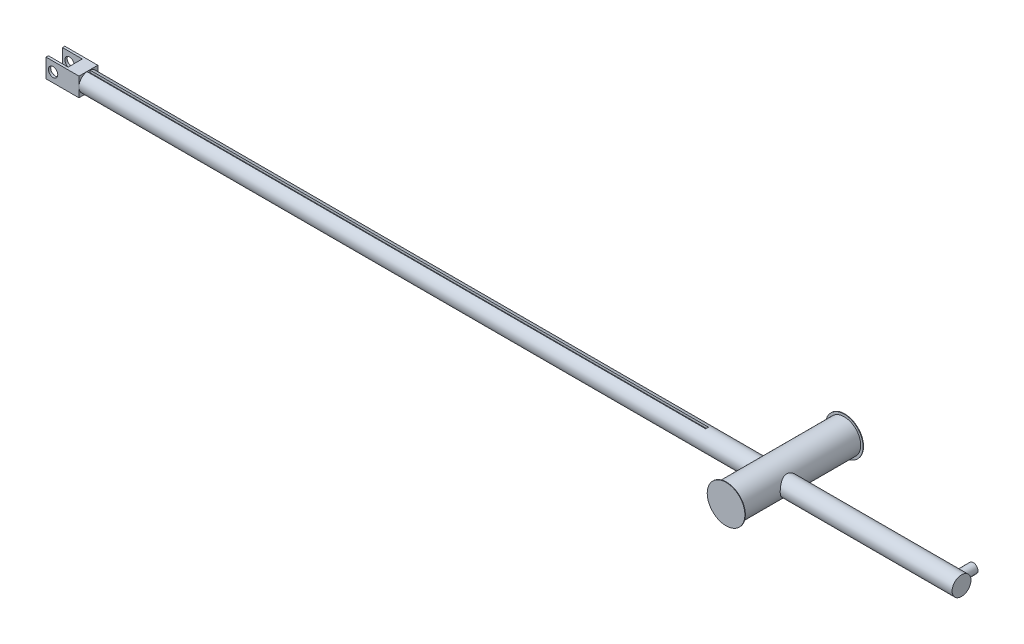
SolidWorks part; units mm, degrees
material "普通碳钢"
ref_plane "前视基准面" through (0, 0, 0) normal (0, 0, 1) x (1, 0, 0)
ref_plane "上视基准面" through (0, 0, 0) normal (0, 1, 0) x (1, 0, 0)
ref_plane "右视基准面" through (0, 0, 0) normal (1, 0, 0) x (0, 0, -1)
sketch "草图1" plane through (0, 0, 0) normal (1, 0, 0) x (0, 0, -1)
  circle A0 centre (0, 0) radius 2
  dimension "D1" = 4
extrude "凸台-拉伸1" add sketch "草图1" along normal blind 192.4
sketch "草图2" plane through (0, 0, 0) normal (0, 0, 1) x (1, 0, 0)
  line L0 (192.4, 0) -> (0, 0) construction
  circle A0 centre (2, 0) radius 1
  dimension "D1" = 2
  dimension "D2" = 2
extrude "凸台-拉伸2" add sketch "草图2" against normal blind 4.5
sketch "草图3" plane through (0, 0, 0) normal (0, 0, 1) x (1, 0, 0)
  circle A0 centre (40, 0) radius 3.5
  dimension "D1" = 7
  dimension "D2" = 40
extrude "凸台-拉伸3" add sketch "草图3" along normal blind 10 and the other way blind 15.1
sketch "草图4" plane through (0, 0, 10) normal (0, 0, 1) x (1, 0, 0)
  circle A0 centre (40, 0) radius 4
  dimension "D1" = 8
extrude "凸台-拉伸4" add sketch "草图4" against normal blind 0.1
sketch "草图5" plane through (0, 0, -15.1) normal (0, 0, -1) x (-1, 0, 0)
  circle A1 centre (-40, 0) radius 4
  circle A2 centre (-40, 0) radius 4
  dimension "D1" = 0
extrude "凸台-拉伸5" add sketch "草图5" along normal blind 0.1
sketch "草图6" plane through (0, 0, 0) normal (0, 1, 0) x (1, 0, 0)
  line L0 (43.5, -2) -> (192.4, -2) construction
  line L1 (192.4, 2) -> (185.4, 2)
  line L2 (192.4, 2) -> (192.4, -2)
  line L3 (192.4, -2) -> (185.4, -2)
  line L4 (185.4, 2) -> (185.4, -2)
  dimension "D1" = 7
extrude "凸台-拉伸6" add sketch "草图6" along normal mid plane 4
sketch "草图7" plane through (0, 0, 0) normal (0, 1, 0) x (1, 0, 0)
  line L0 (192.4, -2) -> (192.4, 2) construction
  line L1 (192.4, 1.5) -> (188.2, 1.5)
  line L2 (192.4, 1.5) -> (192.4, -1.5)
  line L3 (192.4, -1.5) -> (188.2, -1.5)
  line L4 (188.2, 1.5) -> (188.2, -1.5)
  line L5 (185.4, -2) -> (192.4, -2) construction
  dimension "D1" = 3
  dimension "D2" = 0.5
  dimension "D3" = 4.2
extrude "切除-拉伸1" cut sketch "草图7" against normal mid plane 4
sketch "草图8" plane through (0, 0, 0) normal (0, 0, 1) x (1, 0, 0)
  line L0 (192.4, 2) -> (192.4, -2) construction
  line L1 (190.9, 0) -> (192.4, 0) construction
  circle A0 centre (190.9, 0) radius 1
  dimension "D1" = 2
  dimension "D2" = 1.5
extrude "切除-拉伸2" cut sketch "草图8" against normal mid plane 4
sketch "草图9" plane through (0, 2, 0) normal (0, 1, 0) x (1, 0, 0)
  line L0 (185.4, 0) -> (185.4, -2) construction
  line L1 (54, 0.3) -> (185.4, 0.3)
  line L2 (54, 0.3) -> (54, -0.3)
  line L3 (54, -0.3) -> (185.4, -0.3)
  line L4 (185.4, 0.3) -> (185.4, -0.3)
  line L5 (54, 0) -> (0, 0) construction
  dimension "D1" = 0.6
  dimension "D2" = 54
extrude "切除-拉伸3" cut sketch "草图9" against normal blind 0.5
mirror "镜向1" about plane through (0, 0, 0) normal (1, 0, 0) of bodies 115
delete or keep bodies "实体-删除/保留 1" type delete bodies bodies 115
